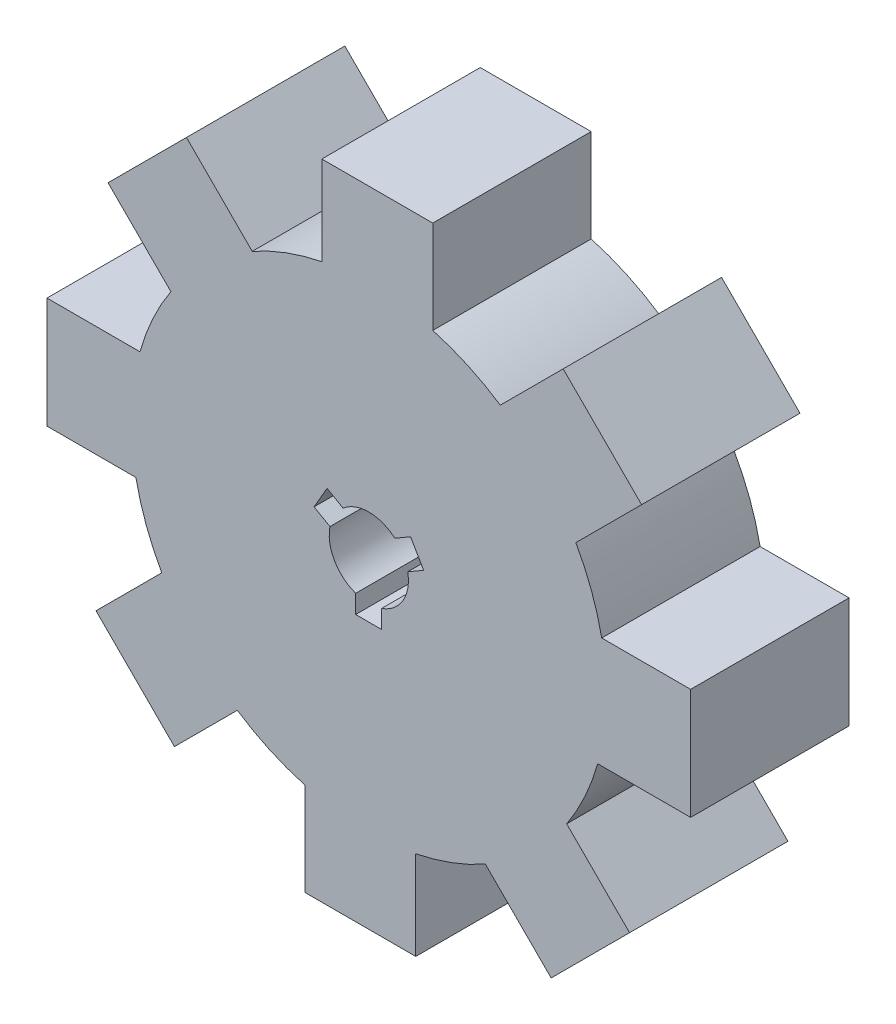
SolidWorks part; units mm, degrees
ref_plane "Front Plane" through (0, 0, 0) normal (0, 0, 1) x (1, 0, 0)
ref_plane "Top Plane" through (0, 0, 0) normal (0, 1, 0) x (1, 0, 0)
ref_plane "Right Plane" through (0, 0, 0) normal (1, 0, 0) x (0, 0, -1)
ref_plane "Plane4"
sketch "Sketch1" plane through (0, 0, 0) normal (0, 0, 1) x (1, 0, 0)
  line L0 (5.1282, 18.3468) -> (5.1282, 25.8035)
  line L1 (5.1282, 25.8035) -> (-3.7641, 25.8035)
  line L2 (-3.7641, 25.8035) -> (-3.7641, 18.6744)
  line L3 (-9.3469, 16.5993) -> (-14.6196, 21.8721)
  line L4 (-14.6196, 21.8721) -> (-20.9074, 15.5843)
  line L5 (-20.9074, 15.5843) -> (-15.8664, 10.5432)
  line L6 (-18.3468, 5.1282) -> (-25.8035, 5.1282)
  line L7 (-25.8035, 5.1282) -> (-25.8035, -3.7641)
  line L8 (-25.8035, -3.7641) -> (-18.6744, -3.7641)
  line L9 (-16.5993, -9.3469) -> (-21.8721, -14.6196)
  line L10 (-21.8721, -14.6196) -> (-15.5843, -20.9074)
  line L11 (-15.5843, -20.9074) -> (-10.5432, -15.8664)
  line L12 (-5.1282, -18.3468) -> (-5.1282, -25.8035)
  line L13 (-5.1282, -25.8035) -> (3.7641, -25.8035)
  line L14 (3.7641, -25.8035) -> (3.7641, -18.6744)
  line L15 (9.3469, -16.5993) -> (14.6196, -21.8721)
  line L16 (14.6196, -21.8721) -> (20.9074, -15.5843)
  line L17 (20.9074, -15.5843) -> (15.8664, -10.5432)
  line L18 (18.3468, -5.1282) -> (25.8035, -5.1282)
  line L19 (25.8035, -5.1282) -> (25.8035, 3.7641)
  line L20 (25.8035, 3.7641) -> (18.6744, 3.7641)
  line L21 (16.5993, 9.3469) -> (21.8721, 14.6196)
  line L22 (21.8721, 14.6196) -> (15.5843, 20.9074)
  line L23 (15.5843, 20.9074) -> (10.5432, 15.8664)
  line L24 (-3.3435, 3.1468) -> (-2.0672, 2.4099)
  line L25 (2.0833, 2.3959) -> (3.3536, 3.1294)
  line L26 (3.3536, 3.1294) -> (4.397, 1.3222)
  line L27 (4.397, 1.3222) -> (3.1206, 0.5853)
  line L28 (1.0333, -3.0022) -> (1.0333, -4.469)
  line L29 (1.0333, -4.469) -> (-1.0534, -4.469)
  line L30 (-1.0534, -4.469) -> (-1.0534, -2.9952)
  line L31 (-3.1166, 0.6062) -> (-4.3869, 1.3396)
  line L32 (-4.3869, 1.3396) -> (-3.3435, 3.1468)
  arc A0 (-3.7641, 18.6744) -> (-9.3469, 16.5993) centre (0, 0) ccw
  arc A1 (-15.8664, 10.5432) -> (-18.3468, 5.1282) centre (0, 0) ccw
  arc A2 (-18.6744, -3.7641) -> (-16.5993, -9.3469) centre (0, 0) ccw
  arc A3 (-10.5432, -15.8664) -> (-5.1282, -18.3468) centre (0, 0) ccw
  arc A4 (3.7641, -18.6744) -> (9.3469, -16.5993) centre (0, 0) ccw
  arc A5 (15.8664, -10.5432) -> (18.3468, -5.1282) centre (0, 0) ccw
  arc A6 (18.6744, 3.7641) -> (16.5993, 9.3469) centre (0, 0) ccw
  arc A7 (10.5432, 15.8664) -> (5.1282, 18.3468) centre (0, 0) ccw
  arc A8 (2.0833, 2.3959) -> (-2.0672, 2.4099) centre (0, 0) ccw
  arc A9 (1.0333, -3.0022) -> (3.1206, 0.5853) centre (0, 0) ccw
  arc A10 (-3.1166, 0.6062) -> (-1.0534, -2.9952) centre (0, 0) ccw
  dimension "D1" = 8.8923
  dimension "D2" = 45
extrude "Extrusion2" add sketch "Sketch1" along normal blind 12.7 contours L23 A7 L0 L1 L2 A0 L3 L4 L5 A1 L6 L7 L8 A2 L9 L10 L11 A3 L12 L13 L14 A4 L15 L16 L17 A5 L18 L19 L20 A6 L21 L22 A10 L31 L32 L24 A8 L25 L26 L27 A9 L28 L29 L30
